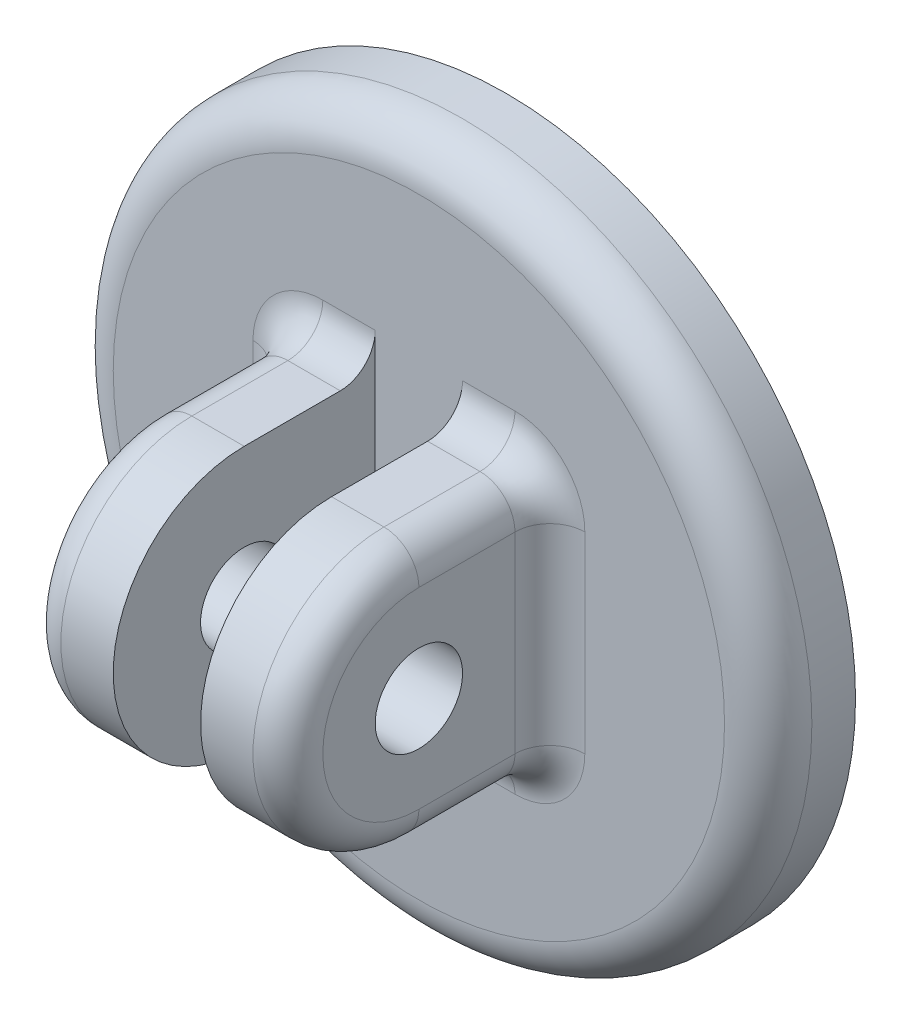
SolidWorks part; units mm, degrees
material "ABS"
ref_plane "Alzado" through (0, 0, 0) normal (0, 0, 1) x (1, 0, 0)
ref_plane "Planta" through (0, 0, 0) normal (0, 1, 0) x (1, 0, 0)
ref_plane "Vista lateral" through (0, 0, 0) normal (1, 0, 0) x (0, 0, -1)
sketch "Croquis1" plane through (0, 0, 0) normal (0, 0, 1) x (1, 0, 0)
  circle A0 centre (0, 0) radius 20
  dimension "D1" = 40
extrude "Saliente-Extruir1" add sketch "Croquis1" along normal blind 5
sketch "Croquis2" plane through (0, 0, 5) normal (0, 0, 1) x (1, 0, 0)
  circle A0 centre (0, 0) radius 2.5
  dimension "D1" = 5
extrude "Cortar-Extruir1" cut sketch "Croquis2" against normal blind 5
sketch "Croquis3" plane through (0, 0, 5) normal (0, 0, 1) x (1, 0, 0)
  line L1 (-2.5, 19.8431) -> (2.5, 19.8431) construction
  line L2 (-2.5, 19.8431) -> (-2.5, -19.8431) construction
  line L3 (-2.5, -19.8431) -> (2.5, -19.8431) construction
  line L4 (2.5, 19.8431) -> (2.5, -19.8431) construction
  line L5 (-2.5, 19.8431) -> (2.5, -19.8431) construction
  line L6 (-2.5, -19.8431) -> (2.5, 19.8431) construction
  line L7 (2.5, -7.5) -> (7.5, -7.5)
  line L8 (2.5, -7.5) -> (2.5, 7.5)
  line L9 (2.5, 7.5) -> (7.5, 7.5)
  line L10 (7.5, -7.5) -> (7.5, 7.5)
  circle A0 centre (0, 0) radius 20 construction
  circle A1 centre (0, 0) radius 2.5 construction
  point P0 (0, 0)
  point P14 (5, -7.5)
  point P15 (5, 7.5)
  dimension "D1" = 7.5
  dimension "D2" = 15
  dimension "D3" = 5
extrude "Saliente-Extruir3" add sketch "Croquis3" along normal blind 15
sketch "Croquis4" plane through (7.5, 0, 0) normal (1, 0, 0) x (0, 0, -1)
  line L0 (-20, -7.5) -> (-20, 7.5) construction
  line L1 (-20, 7.5) -> (-5, 7.5) construction
  line L2 (-20, -7.5) -> (-5, -7.5) construction
  circle A0 centre (-12.5, 0) radius 2.5
  arc A1 (-12.5, 7.5) -> (-12.5, -7.5) centre (-12.5, 0) ccw
  line M2 (-5, 7.5) -> (-20, 7.5)
  line M3 (-20, 7.5) -> (-20, -7.5)
  line M4 (-20, -7.5) -> (-5, -7.5)
  dimension "D1" = 5
  dimension "D2" = 7.5
  dimension "D3" = 7.5
extrude "Cortar-Extruir2" cut sketch "Croquis4" against normal blind 5 contours A1 M3 M4 | A1 M2 M3 | A0
mirror "Simetría1" about plane through (0, 0, 0) normal (1, 0, 0) of bodies 107
fillet "Fillet1" radius 2 12 edges at (5, 7.5, 5) (-5, 7.5, 5) (7.5, 0, 5) (-7.5, 0, 5) (7.5, 7.5, 8.75) (7.5, -7.5, 8.75) (-7.5, 7.5, 8.75) (-7.5, -7.5, 8.75) (-5, -7.5, 5) (5, -7.5, 5) (7.5, 0, 20) (-7.5, 0, 20)
fillet "Fillet2" radius 2.5 1 edges at (20, 0, 5)
